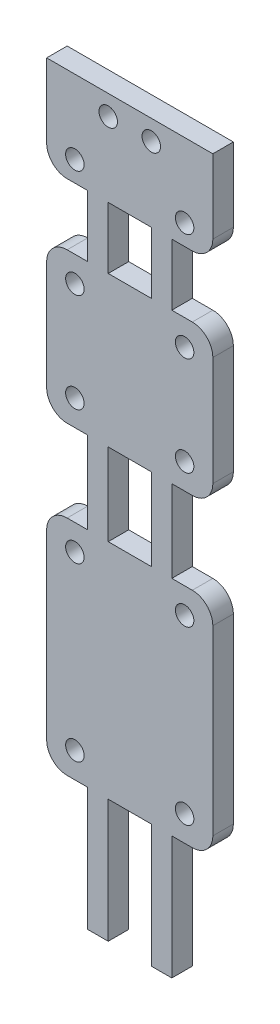
SolidWorks part; units mm, degrees
ref_plane "Front Plane" through (0, 0, 0) normal (0, 0, 1) x (1, 0, 0)
ref_plane "Top Plane" through (0, 0, 0) normal (0, 1, 0) x (1, 0, 0)
ref_plane "Right Plane" through (0, 0, 0) normal (1, 0, 0) x (0, 0, -1)
sketch "Sketch1" plane through (0, 0, 0) normal (0, 0, 1) x (1, 0, 0)
  line L0 (0, 1.5) -> (0, 14) construction
  line L1 (16.2, 1.5) -> (16.2, 14) construction
  line L2 (2, 47.74) -> (4, 47.74)
  line L3 (0, 1.5) -> (16.2, 1.5) construction
  line L4 (0, 14) -> (4, 14) construction
  line L5 (2, 26) -> (4, 26)
  line L6 (16.2, 85.59) -> (0, 85.59)
  line L7 (2, 70.385) -> (4, 70.385)
  line L8 (2, 55.74) -> (4, 55.74)
  line L9 (0, 28) -> (0, 45.74)
  line L10 (2, 76.385) -> (4, 76.385)
  line L11 (16.2, 28) -> (16.2, 45.74)
  line L12 (16.2, 57.74) -> (16.2, 68.385)
  line L13 (0, 57.74) -> (0, 68.385)
  line L14 (16.2, 78.385) -> (16.2, 85.59)
  line L15 (0, 78.385) -> (0, 85.59)
  line L16 (6, 70.385) -> (6, 76.385)
  line L17 (4, 55.74) -> (4, 47.74)
  line L18 (4, 70.385) -> (4, 76.385)
  line L19 (6, 55.74) -> (6, 47.74)
  line L20 (4, 26) -> (4, 14)
  line L21 (6, 26) -> (6, 14)
  line L22 (8.1, 1.5) -> (8.1, 85.59) construction
  line L23 (10.2, 26) -> (10.2, 14)
  line L24 (12.2, 26) -> (12.2, 14)
  line L25 (10.2, 55.74) -> (10.2, 47.74)
  line L26 (12.2, 55.74) -> (12.2, 47.74)
  line L27 (10.2, 70.385) -> (10.2, 76.385)
  line L28 (12.2, 70.385) -> (12.2, 76.385)
  line L29 (6, 26) -> (10.2, 26)
  line L30 (6, 14) -> (10.2, 14) construction
  line L31 (12.2, 14) -> (16.2, 14) construction
  line L32 (12.2, 26) -> (14.2, 26)
  line L33 (12.2, 47.74) -> (14.2, 47.74)
  line L34 (6, 47.74) -> (10.2, 47.74)
  line L35 (12.2, 76.385) -> (14.2, 76.385)
  line L36 (6, 76.385) -> (10.2, 76.385)
  line L37 (6, 70.385) -> (10.2, 70.385)
  line L38 (12.2, 70.385) -> (14.2, 70.385)
  line L39 (12.2, 55.74) -> (14.2, 55.74)
  line L40 (6, 55.74) -> (10.2, 55.74)
  line L41 (4, 14) -> (6, 14)
  line L42 (10.2, 14) -> (12.2, 14)
  circle A0 centre (13.45, 45.24) radius 0.9
  circle A1 centre (2.75, 67.885) radius 0.9
  circle A2 centre (13.45, 58.24) radius 0.9
  circle A3 centre (13.45, 78.385) radius 0.9
  circle A4 centre (2.75, 28.5) radius 0.9
  circle A5 centre (2.75, 78.385) radius 0.9
  circle A6 centre (2.75, 58.24) radius 0.9
  circle A7 centre (2.85, 11.5) radius 0.9 construction
  circle A8 centre (13.35, 11.5) radius 0.9 construction
  circle A9 centre (13.35, 5.5) radius 0.9 construction
  circle A10 centre (2.85, 5.5) radius 0.9 construction
  circle A11 centre (6, 83.635) radius 0.9
  circle A12 centre (13.45, 28.5) radius 0.9
  circle A13 centre (13.45, 67.885) radius 0.9
  circle A14 centre (10.2, 83.635) radius 0.9
  circle A15 centre (2.75, 45.24) radius 0.9
  arc A16 (0, 28) -> (2, 26) centre (2, 28) ccw
  arc A17 (16.2, 28) -> (14.2, 26) centre (14.2, 28) cw
  arc A18 (16.2, 45.74) -> (14.2, 47.74) centre (14.2, 45.74) ccw
  arc A19 (0, 45.74) -> (2, 47.74) centre (2, 45.74) cw
  arc A20 (0, 57.74) -> (2, 55.74) centre (2, 57.74) ccw
  arc A21 (16.2, 57.74) -> (14.2, 55.74) centre (14.2, 57.74) cw
  arc A22 (0, 68.385) -> (2, 70.385) centre (2, 68.385) cw
  arc A23 (16.2, 68.385) -> (14.2, 70.385) centre (14.2, 68.385) ccw
  arc A24 (16.2, 78.385) -> (14.2, 76.385) centre (14.2, 78.385) cw
  arc A25 (2, 76.385) -> (0, 78.385) centre (2, 78.385) cw
  point P77 (0, 26)
  point P80 (16.2, 26)
  point P83 (16.2, 47.74)
  point P86 (0, 47.74)
  point P89 (0, 55.74)
  point P92 (16.2, 55.74)
  point P95 (0, 70.385)
  point P98 (16.2, 70.385)
  point P101 (16.2, 76.385)
  point P104 (0, 76.385)
  dimension "D1" = 4
  dimension "D40" = 2
  dimension "D41" = 1.8
  dimension "D2" = 4
  dimension "D3" = 6
  dimension "D4" = 6
  dimension "D5" = 2.5
  dimension "D6" = 12
  dimension "D7" = 2.85
  dimension "D8" = 2.85
  dimension "D9" = 2.85
  dimension "D10" = 16.2
  dimension "D11" = 21.74
  dimension "D12" = 2.75
  dimension "D13" = 2.75
  dimension "D14" = 2.75
  dimension "D15" = 2.75
  dimension "D16" = 2.5
  dimension "D17" = 2.5
  dimension "D18" = 2.5
  dimension "D19" = 2.5
  dimension "D20" = 8
  dimension "D21" = 14.645
  dimension "D22" = 2.75
  dimension "D23" = 2.75
  dimension "D24" = 2.5
  dimension "D25" = 2.5
  dimension "D26" = 2.5
  dimension "D27" = 2.5
  dimension "D28" = 2.75
  dimension "D29" = 2.75
  dimension "D30" = 6
  dimension "D31" = 9.205
  dimension "D32" = 2.75
  dimension "D33" = 6
  dimension "D34" = 2
  dimension "D35" = 7.25
  dimension "D36" = 2
  dimension "D37" = 7.25
  dimension "D38" = 6
  dimension "D39" = 2.75
extrude "Boss-Extrude1" add sketch "Sketch1" along normal blind 2
sketch "Sketch2" plane through (0, 0, 2) normal (0, 0, 1) x (1, 0, 0)
  line L0 (4, 76.385) -> (12.2, 76.385)
  line L1 (12.2, 76.385) -> (12.2, 70.385)
  line L2 (12.2, 70.385) -> (4, 70.385)
  line L3 (4, 70.385) -> (4, 76.385)
  line L4 (4, 55.74) -> (12.2, 55.74)
  line L5 (12.2, 55.74) -> (12.2, 47.74)
  line L6 (12.2, 47.74) -> (4, 47.74)
  line L7 (4, 47.74) -> (4, 55.74)
  line L8 (4, 26) -> (12.2, 26)
  line L9 (12.2, 26) -> (12.2, 14)
  line L10 (12.2, 14) -> (4, 14)
  line L11 (4, 14) -> (4, 26)
extrude "Cut-Extrude1" [suppressed] cut sketch "Sketch2" against normal up to surface (2 mm away)
equation "\"D11@Sketch1\"= \"HL@parametersSketch@prostheticParameters.SLDPRT\" * 0.204 - 4 - 12 'Pinky PIP Length"
equation "\"D21@Sketch1\"= \"HL@parametersSketch@prostheticParameters.SLDPRT\" * 0.117 - 4 - 3 'Pinky MIP Length"
equation "\"D31@Sketch1\"= \"HL@parametersSketch@prostheticParameters.SLDPRT\" * 0.093 - 3 - 5'Pinky DIP Length"
equation "\"D10@Sketch1\"= \"fingerWidth@parametersSketch@prostheticParameters.SLDPRT\"'Pinky Width"
equation "\"D41@Sketch1\"= 1.5 + \"tol1@parametersSketch@prostheticParameters.SLDPRT\""
